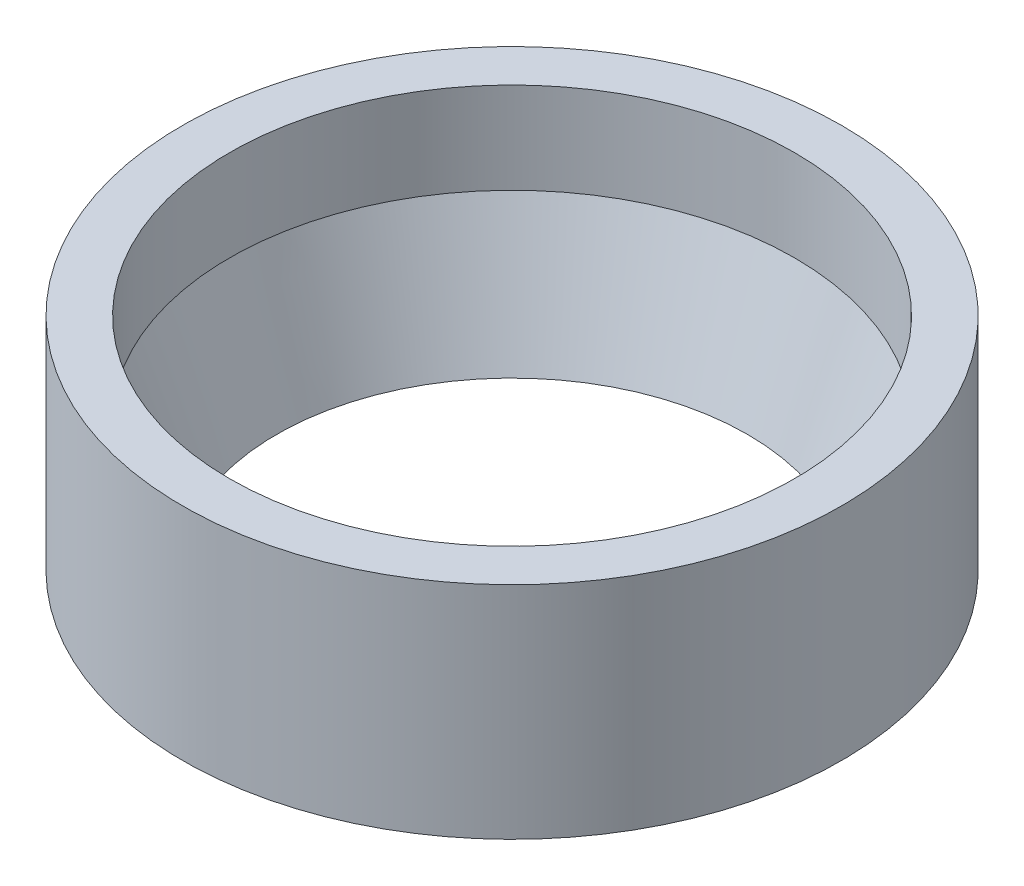
SolidWorks part; units mm, degrees
material "Custom Plastic"
ref_plane "Front Plane" through (0, 0, 0) normal (0, 0, 1) x (1, 0, 0)
ref_plane "Top Plane" through (0, 0, 0) normal (0, 1, 0) x (1, 0, 0)
ref_plane "Right Plane" through (0, 0, 0) normal (1, 0, 0) x (0, 0, -1)
sketch "Sketch1" plane through (0, 0, 0) normal (0, 0, 1) x (1, 0, 0)
  line L0 (0, 0) -> (0, 71.2261) construction
  line L1 (0, 0) -> (-38.1, 0) construction
  line L2 (-38.1, 0) -> (-38.1, -12.2969)
  line L3 (-38.1, -12.2969) -> (-31.75, -29.7434)
  line L4 (-31.75, -29.7434) -> (-44.45, -29.7434)
  line L5 (-38.1, 0) -> (-44.45, 0)
  line L6 (-44.45, 0) -> (-44.45, -29.7434)
  dimension "D1" = 38.1
  dimension "D2" = 6.35
  dimension "D3" = 31.75
  dimension "D4" = 29.7434
  dimension "D5" = 70
revolve "Revolve1" add sketch "Sketch1" angle 360 about L0
